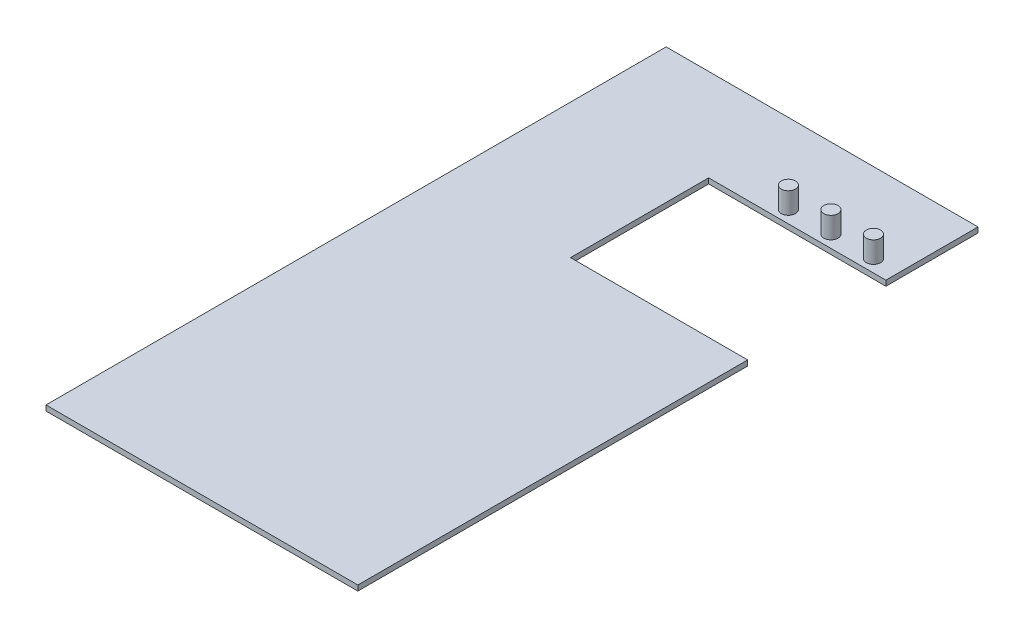
SolidWorks part; units mm, degrees
ref_plane "Front Plane" through (0, 0, 0) normal (0, 0, 1) x (1, 0, 0)
ref_plane "Top Plane" through (0, 0, 0) normal (0, 1, 0) x (1, 0, 0)
ref_plane "Right Plane" through (0, 0, 0) normal (1, 0, 0) x (0, 0, -1)
sketch "Sketch1" plane through (0, 0, 0) normal (0, 1, 0) x (1, 0, 0)
  line L1 (44, 87.5) -> (-44, 87.5)
  line L2 (44, 87.5) -> (44, -87.5)
  line L3 (44, -87.5) -> (-44, -87.5)
  line L4 (-44, 87.5) -> (-44, -87.5)
  line L5 (44, 87.5) -> (-44, -87.5) construction
  line L6 (44, -87.5) -> (-44, 87.5) construction
  point P0 (0, 0)
  dimension "D1" = 175
  dimension "D2" = 88
extrude "Boss-Extrude1" add sketch "Sketch1" along normal blind 1.5
sketch "Sketch2" plane through (0, 1.5, 0) normal (0, 1, 0) x (1, 0, 0)
  line L0 (44, -87.5) -> (44, 87.5) construction
  line L1 (44, 22.5) -> (-6, 22.5)
  line L2 (44, 22.5) -> (44, 61.5)
  line L3 (44, 61.5) -> (-6, 61.5)
  line L4 (-6, 22.5) -> (-6, 61.5)
  line L5 (-44, -87.5) -> (44, -87.5) construction
  dimension "D1" = 110
  dimension "D2" = 39
  dimension "D3" = 50
extrude "Cut-Extrude1" cut sketch "Sketch2" against normal blind 1.5
sketch "Sketch3" plane through (0, 1.5, 0) normal (0, 1, 0) x (1, 0, 0)
  line L0 (44, 61.5) -> (-6, 61.5) construction
  line L1 (44, 61.5) -> (44, 87.5) construction
  circle A0 centre (37, 65) radius 2
  circle A1 centre (25, 65) radius 2
  circle A2 centre (13, 65) radius 2
  dimension "D3" = 4
  dimension "D1" = 3.5
  dimension "D2" = 7
  dimension "D4" = 12
  dimension "D5" = 12
extrude "Boss-Extrude2" add sketch "Sketch3" along normal blind 6
